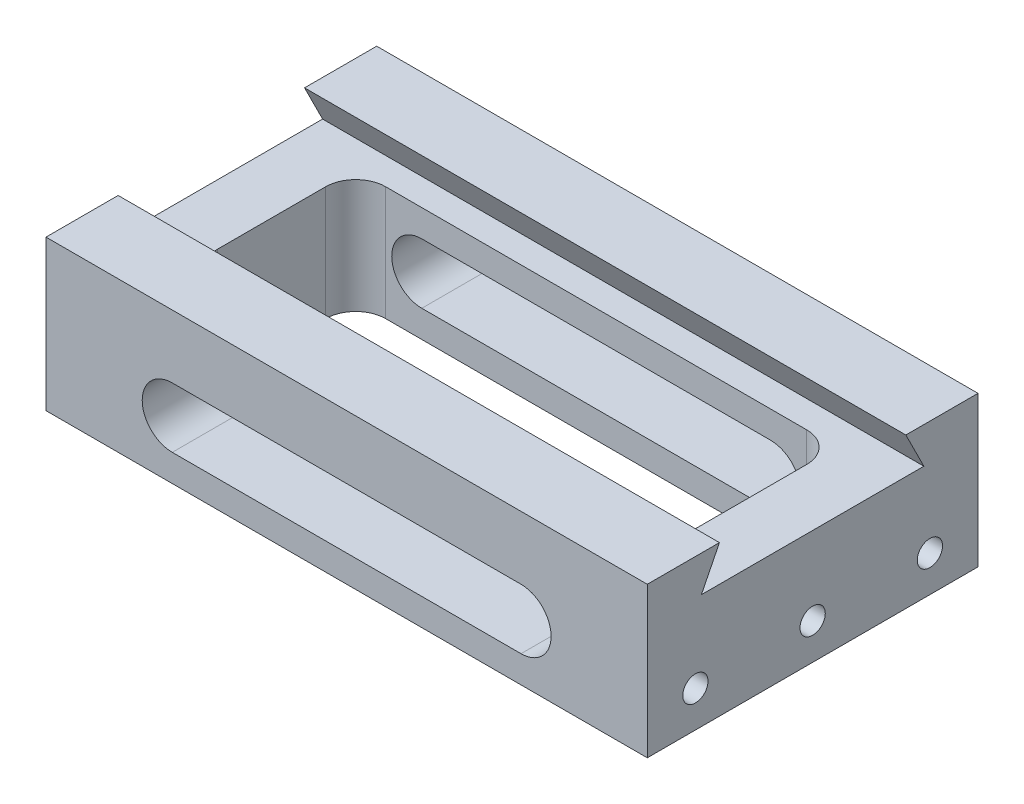
SolidWorks part; units mm, degrees
material "AISI 316 Stainless Steel Sheet (SS)"
ref_plane "Front Plane" through (0, 0, 0) normal (0, 0, 1) x (1, 0, 0)
ref_plane "Top Plane" through (0, 0, 0) normal (0, 1, 0) x (1, 0, 0)
ref_plane "Right Plane" through (0, 0, 0) normal (1, 0, 0) x (0, 0, -1)
sketch "Sketch1" plane through (0, 0, 0) normal (0, 1, 0) x (1, 0, 0)
  line L1 (-50, -27.5) -> (50, -27.5)
  line L2 (-50, -27.5) -> (-50, 27.5)
  line L3 (-50, 27.5) -> (50, 27.5)
  line L4 (50, -27.5) -> (50, 27.5)
  line L5 (-50, -27.5) -> (50, 27.5) construction
  line L6 (-50, 27.5) -> (50, -27.5) construction
  point P0 (0, 0)
  dimension "D1" = 100
  dimension "D2" = 55
extrude "Boss-Extrude1" add sketch "Sketch1" along normal blind 25
sketch "Sketch2" plane through (0, 25, 0) normal (0, 1, 0) x (1, 0, 0)
  line L1 (-35, -14) -> (35, -14)
  line L2 (-40, -9) -> (-40, 9)
  line L3 (-35, 14) -> (35, 14)
  line L4 (40, -9) -> (40, 9)
  line L5 (-40, -14) -> (40, 14) construction
  line L6 (-40, 14) -> (40, -14) construction
  arc A0 (-35, -14) -> (-40, -9) centre (-35, -9) cw
  arc A1 (35, -14) -> (40, -9) centre (35, -9) ccw
  arc A2 (35, 14) -> (40, 9) centre (35, 9) cw
  arc A3 (-40, 9) -> (-35, 14) centre (-35, 9) cw
  point P0 (0, 0)
  dimension "D3" = 5
  dimension "D1" = 80
  dimension "D2" = 28
extrude "Cut-Extrude1" cut sketch "Sketch2" against normal through all
sketch "Sketch3" plane through (50, 0, 0) normal (1, 0, 0) x (0, 0, -1)
  line L0 (15.5, 25) -> (18.5, 19)
  line L1 (-27.5, 25) -> (27.5, 25) construction
  line L2 (18.5, 19) -> (-18.5, 19)
  line L3 (0, 25) -> (0, 1.9451) construction
  line L4 (27.5, 25) -> (27.5, 0) construction
  line L5 (-15.5, 25) -> (15.5, 25)
  line L6 (-15.5, 25) -> (-18.5, 19)
  point P13 (0, 19)
  dimension "D1" = 12
  dimension "D2" = 9
  dimension "D3" = 6
extrude "Cut-Extrude2" cut sketch "Sketch3" against normal through all
sketch "Sketch4" plane through (0, 0, 27.5) normal (0, 0, 1) x (1, 0, 0)
  line L0 (-29, 9.5) -> (29, 9.5) construction
  line L1 (-29, 14.5) -> (29, 14.5)
  line L2 (-29, 4.5) -> (29, 4.5)
  line L3 (-50, 0) -> (50, 0) construction
  arc A0 (-29, 14.5) -> (-29, 4.5) centre (-29, 9.5) ccw
  arc A1 (29, 4.5) -> (29, 14.5) centre (29, 9.5) ccw
  point P2 (0, 9.5)
  dimension "D2" = 5
  dimension "D1" = 58
  dimension "D3" = 9.5
extrude "Cut-Extrude3" cut sketch "Sketch4" against normal through all
hole_wizard "M5x0.8 Tapped Hole1" positions "Sketch6" profile "Sketch7" tap size "M5x0.8" standard "ANSI Metric"
sketch "Sketch6" plane through (50, 0, 0) normal (1, 0, 0) x (0, 0, -1)
  line L0 (27.5, 25) -> (27.5, 0) construction
  line L1 (-27.5, 25) -> (-27.5, 0) construction
  line L2 (-27.5, 0) -> (27.5, 0) construction
  point P0 (-19.5, 6)
  point P2 (0, 6)
  point P4 (19.5, 6)
  dimension "D1" = 8
  dimension "D2" = 8
  dimension "D3" = 6
sketch "Sketch7" plane through (50, 6, 19.5) normal (0, 1, 0) x (0, 0, -1)
  line L0 (0, 0) -> (0, 8.7618)
  line L1 (0, 8.7618) -> (2.1, 7.5)
  line L2 (2.1, 7.5) -> (2.1, 0)
  line L5 (2.1, 0) -> (0, 0)
  line L10 (0, 8.7618) -> (-2.1, 7.5) construction
  line L11 (0, -6.35) -> (0, 107.95) construction
  dimension "Tap Drill Dia." = 4.2
  dimension "Tap Drill Depth" = 7.5
  dimension "Drill Angle" = 118
cosmetic thread "Hole Thread1" parameters "D1"=10, "D2"=5
cosmetic thread "Hole Thread2" parameters "D1"=10, "D2"=5
cosmetic thread "Hole Thread3" parameters "D1"=10, "D2"=5
mirror "Mirror1" about plane through (0, 0, 0) normal (1, 0, 0) of "M5x0.8 Tapped Hole1"
cosmetic thread "Hole Thread4" parameters "D1"=10, "D2"=5
cosmetic thread "Hole Thread5" parameters "D1"=10, "D2"=5
cosmetic thread "Hole Thread6" parameters "D1"=10, "D2"=5
